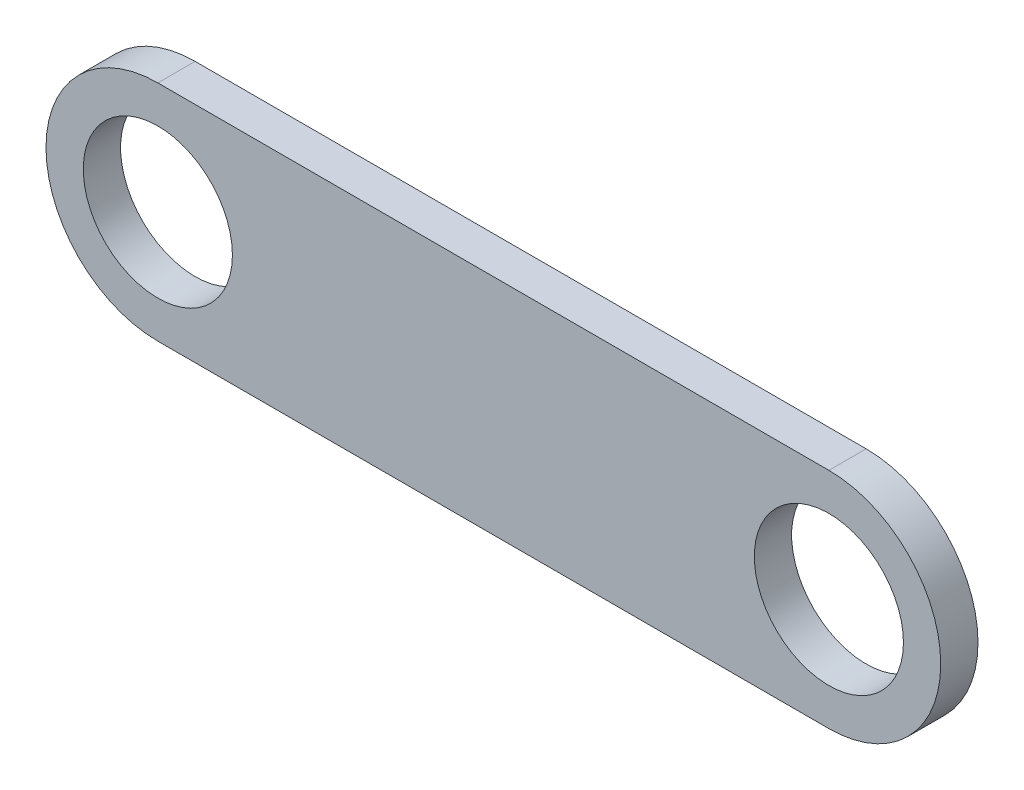
SolidWorks part; units mm, degrees
ref_plane "Alzado" through (0, 0, 0) normal (0, 0, 1) x (1, 0, 0)
ref_plane "Planta" through (0, 0, 0) normal (0, 1, 0) x (1, 0, 0)
ref_plane "Vista lateral" through (0, 0, 0) normal (1, 0, 0) x (0, 0, -1)
sketch "Croquis1" plane through (0, 0, 0) normal (0, 0, 1) x (1, 0, 0)
  line L1 (-27.0414, 12.754) -> (62.9586, 12.754)
  line L3 (-27.0414, -17.246) -> (62.9586, -17.246)
  arc A0 (-27.0414, 12.754) -> (-27.0414, -17.246) centre (-27.0414, -2.246) ccw
  arc A1 (62.9586, -17.246) -> (62.9586, 12.754) centre (62.9586, -2.246) ccw
  circle A2 centre (-27.0414, -2.246) radius 10
  circle A3 centre (62.9586, -2.246) radius 10
  dimension "D3" = 20
  dimension "D4" = 20
  dimension "D1" = 90
  dimension "D2" = 30
extrude "Saliente-Extruir1" add sketch "Croquis1" along normal blind 5
